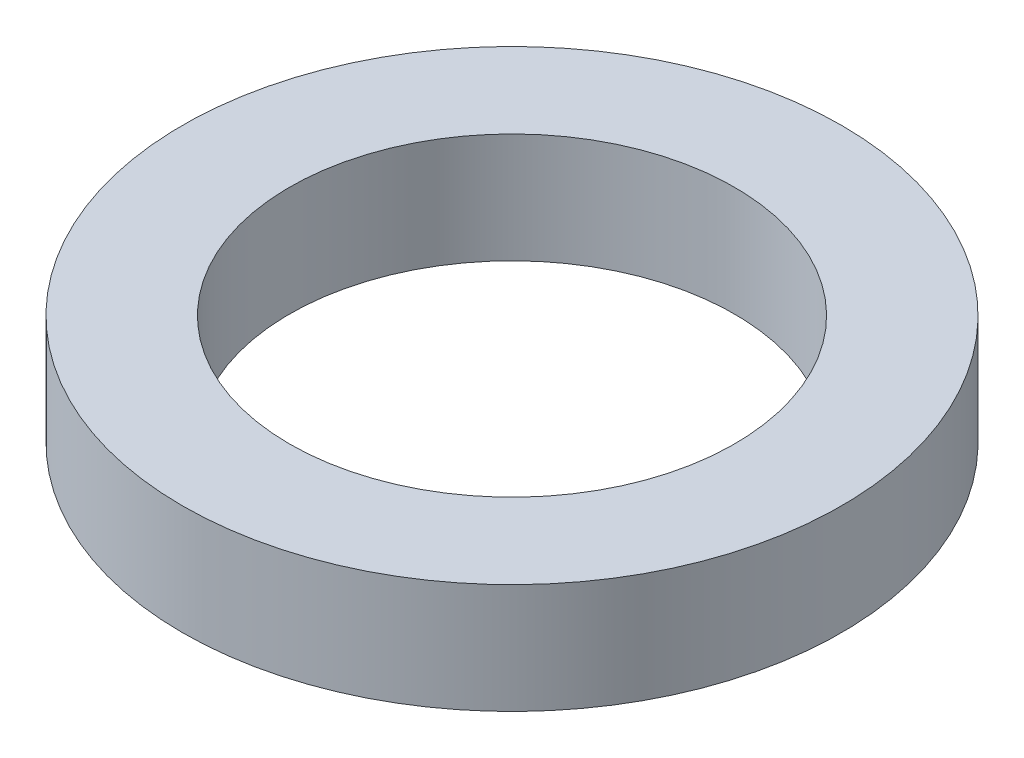
SolidWorks part; units mm, degrees
ref_plane "Front Plane" through (0, 0, 0) normal (0, 0, 1) x (1, 0, 0)
ref_plane "Top Plane" through (0, 0, 0) normal (0, 1, 0) x (1, 0, 0)
ref_plane "Right Plane" through (0, 0, 0) normal (1, 0, 0) x (0, 0, -1)
sketch "Sketch1" plane through (0, 0, 0) normal (0, 1, 0) x (1, 0, 0)
  circle A0 centre (0, 0) radius 4.05
  circle A1 centre (0, 0) radius 6
  dimension "D1" = 8.1
  dimension "D2" = 12
extrude "Boss-Extrude1" add sketch "Sketch1" along normal blind 2
